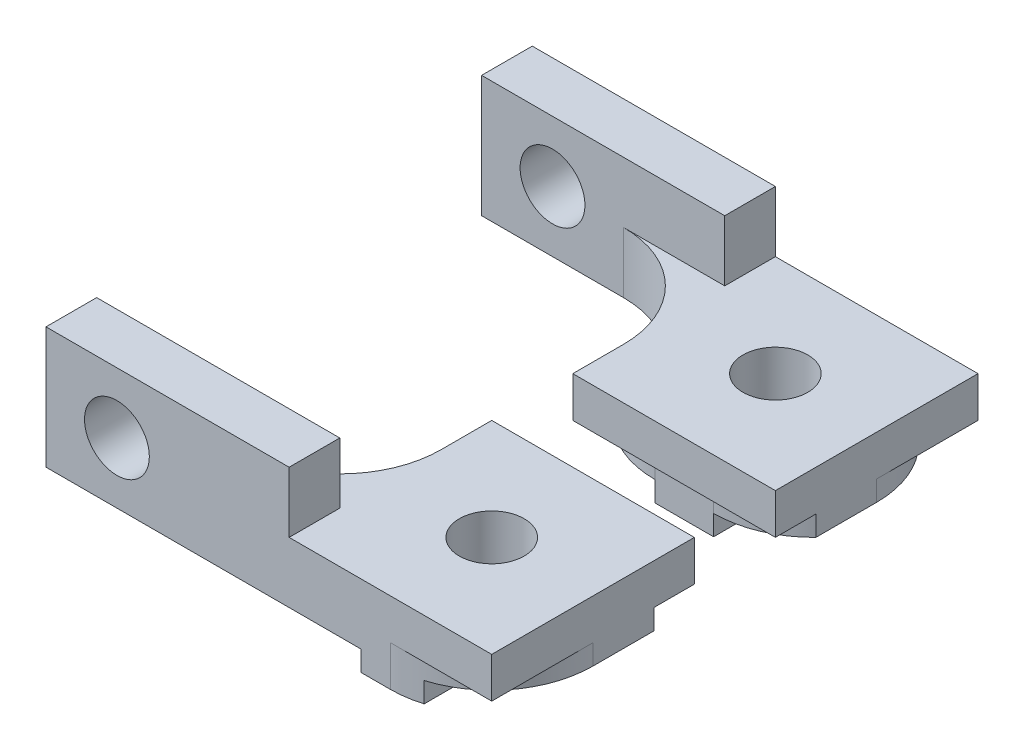
SolidWorks part; units mm, degrees
ref_plane "Front Plane" through (0, 0, 0) normal (0, 0, 1) x (1, 0, 0)
ref_plane "Top Plane" through (0, 0, 0) normal (0, 1, 0) x (1, 0, 0)
ref_plane "Right Plane" through (0, 0, 0) normal (1, 0, 0) x (0, 0, -1)
sketch "Sketch1" plane through (0, 0, 0) normal (0, 0, 1) x (1, 0, 0)
  line L0 (0, 0) -> (-3.55, 0)
  line L1 (-3.55, 0) -> (-3.55, -1)
  line L2 (-3.55, -1) -> (-6.45, -1)
  line L3 (-6.45, -1) -> (-6.45, 0)
  line L4 (-6.45, 0) -> (-22, 0)
  line L5 (0, 0) -> (0, 3)
  line L6 (0, 3) -> (-10, 3)
  line L7 (-10, 3) -> (-10, 6)
  line L8 (-10, 6) -> (-22, 6)
  line L9 (-22, 6) -> (-22, 0)
  circle A0 centre (-18.5, 3) radius 1.6
  point P0 (-9.8146, 4.752)
  point P16 (4.5597, 0)
  point P17 (-2.5548, -1)
  point P18 (4.4431, 0)
  dimension "D4" = 3.2
  dimension "D1" = 2.9
  dimension "D2" = 3.55
  dimension "D3" = 1
  dimension "D5" = 8.5
  dimension "D6" = 12
  dimension "D7" = 3
  dimension "D8" = 10
  dimension "D9" = 3
  dimension "D10" = 6
extrude "Main" add sketch "Sketch1" along normal blind 10
sketch "Sketch2" plane through (0, 3, 0) normal (0, 1, 0) x (1, 0, 0)
  line L0 (0, -10) -> (-10, -10) construction
  line L1 (0, -10) -> (0, 0) construction
  circle A0 centre (-5, -5) radius 1.6
  dimension "D1" = 3.2
  dimension "D2" = 5
  dimension "D3" = 5
extrude "TopHole" cut sketch "Sketch2" against normal through all
sketch "Sketch3" plane through (0, 6, 0) normal (0, 1, 0) x (1, 0, 0)
  line L0 (-22, -10) -> (-22, 0) construction
  line L1 (-22, -7.5) -> (-10, -7.5)
  line L2 (-22, -7.5) -> (-22, 0)
  line L3 (-22, 0) -> (-10, 0)
  line L4 (-10, -7.5) -> (-10, 0)
  line L5 (-10, -10) -> (-22, -10) construction
  dimension "D1" = 2.5
extrude "Cut-Extrude2" cut sketch "Sketch3" against normal through all
fillet "Fillet1" radius 5 1 edges at (-10, 1.5, 7.5)
sketch "Sketch5" plane through (0, -1, 0) normal (0, -1, 0) x (1, 0, 0)
  line L0 (-3.55, 0.5) -> (-6.45, 0.5)
  line L2 (0, 10) -> (0, 0) construction
  line L3 (-10, 2.5) -> (-10, 0) construction
  line L4 (-10, 2) -> (-10, 0)
  line L5 (-10, 0) -> (0, 0)
  line L6 (0, 0) -> (0, 2)
  line L9 (-6.45, 4.3236) -> (-6.45, 0) construction
  line L10 (-3.55, 4.3236) -> (-3.55, 0) construction
  line L12 (-6.45, 10) -> (-3.55, 10) construction
  line L13 (0, 5) -> (0, 10)
  line L14 (0, 10) -> (-5, 10)
  arc A0 (-3.55, 0.5) -> (0, 2) centre (-3.55, 5.4508) ccw
  arc A1 (-6.45, 0.5) -> (-10, 2) centre (-6.45, 5.4508) cw
  arc A3 (-5, 10) -> (0, 5) centre (-5, 5) cw
  point P1 (0, 5)
  dimension "D3" = 5
  dimension "D1" = 0.5
  dimension "D2" = 2
extrude "Cut-Extrude5" cut sketch "Sketch5" against normal blind 2
ref_plane "Plane2" through (0, 0, -2) normal (0, 0, 1) x (1, 0, 0)
mirror "Mirror5" about plane through (0, 0, -2) normal (0, 0, 1) of bodies 107
